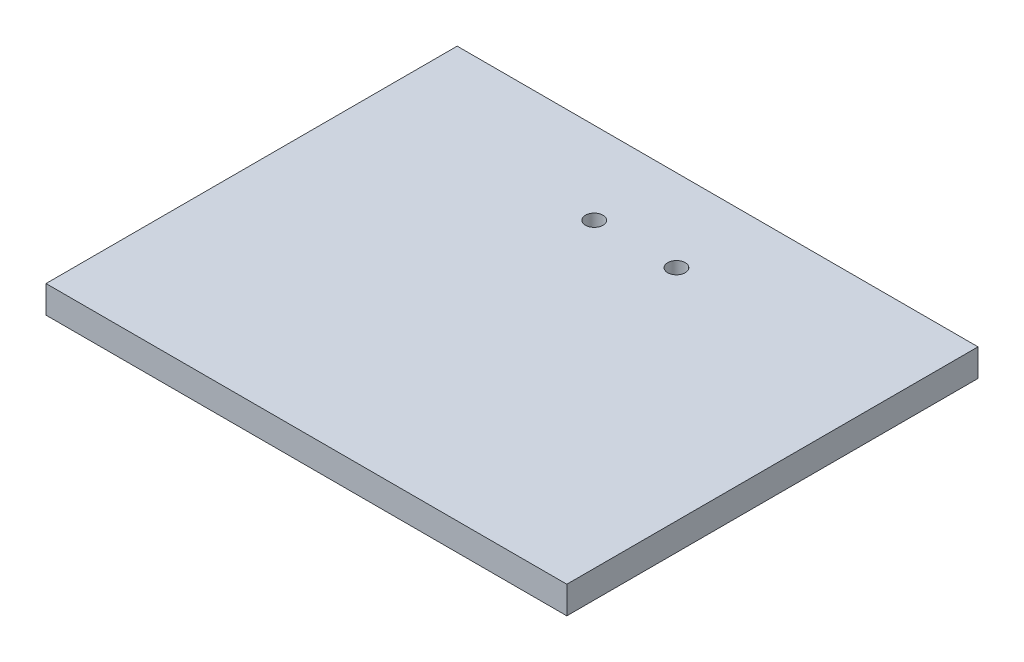
SolidWorks part; units mm, degrees
ref_plane "Front Plane" through (0, 0, 0) normal (0, 0, 1) x (1, 0, 0)
ref_plane "Top Plane" through (0, 0, 0) normal (0, 1, 0) x (1, 0, 0)
ref_plane "Right Plane" through (0, 0, 0) normal (1, 0, 0) x (0, 0, -1)
sketch "Sketch1" plane through (0, 0, 0) normal (0, 1, 0) x (1, 0, 0)
  line L1 (-47.5, -37.5) -> (47.5, -37.5)
  line L2 (-47.5, -37.5) -> (-47.5, 37.5)
  line L3 (-47.5, 37.5) -> (47.5, 37.5)
  line L4 (47.5, -37.5) -> (47.5, 37.5)
  line L5 (-47.5, -37.5) -> (47.5, 37.5) construction
  line L6 (-47.5, 37.5) -> (47.5, -37.5) construction
  point P0 (0, 0)
  dimension "D1" = 75
  dimension "D2" = 95
extrude "Boss-Extrude1" add sketch "Sketch1" along normal blind 5
sketch "Sketch2" plane through (0, 0, 0) normal (0, -1, 0) x (-1, 0, 0)
  line L0 (0, 37.5) -> (0, 22.5) construction
  line L1 (-47.5, 37.5) -> (47.5, 37.5) construction
  line L2 (0, 22.5) -> (-7.5, 22.5) construction
  circle A0 centre (-7.5, 22.5) radius 1.6
  circle A1 centre (7.5, 22.5) radius 1.6
  dimension "D3" = 3.2
  dimension "D1" = 15
  dimension "D2" = 7.5
extrude "Cut-Extrude1" cut sketch "Sketch2" against normal up to next
